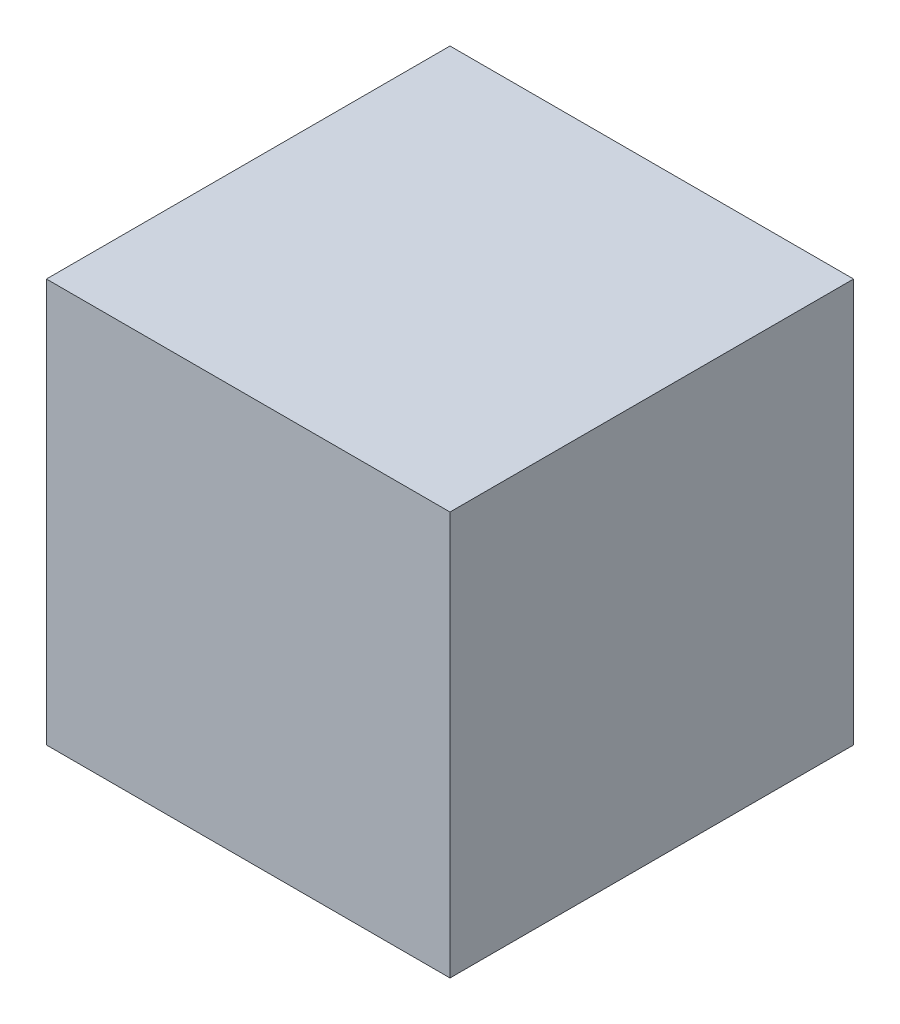
SolidWorks part; units mm, degrees
ref_plane "前视基准面" through (0, 0, 0) normal (0, 0, 1) x (1, 0, 0)
ref_plane "上视基准面" through (0, 0, 0) normal (0, 1, 0) x (1, 0, 0)
ref_plane "右视基准面" through (0, 0, 0) normal (1, 0, 0) x (0, 0, -1)
sketch "草图1" plane through (0, 0, 0) normal (1, 0, 0) x (0, 0, -1)
  line L1 (0, 0) -> (40, 0)
  line L2 (0, 0) -> (0, 40)
  line L3 (0, 40) -> (40, 40)
  line L4 (40, 0) -> (40, 40)
  dimension "D1" = 40
  dimension "D2" = 40
extrude "凸台-拉伸1" add sketch "草图1" along normal blind 40
